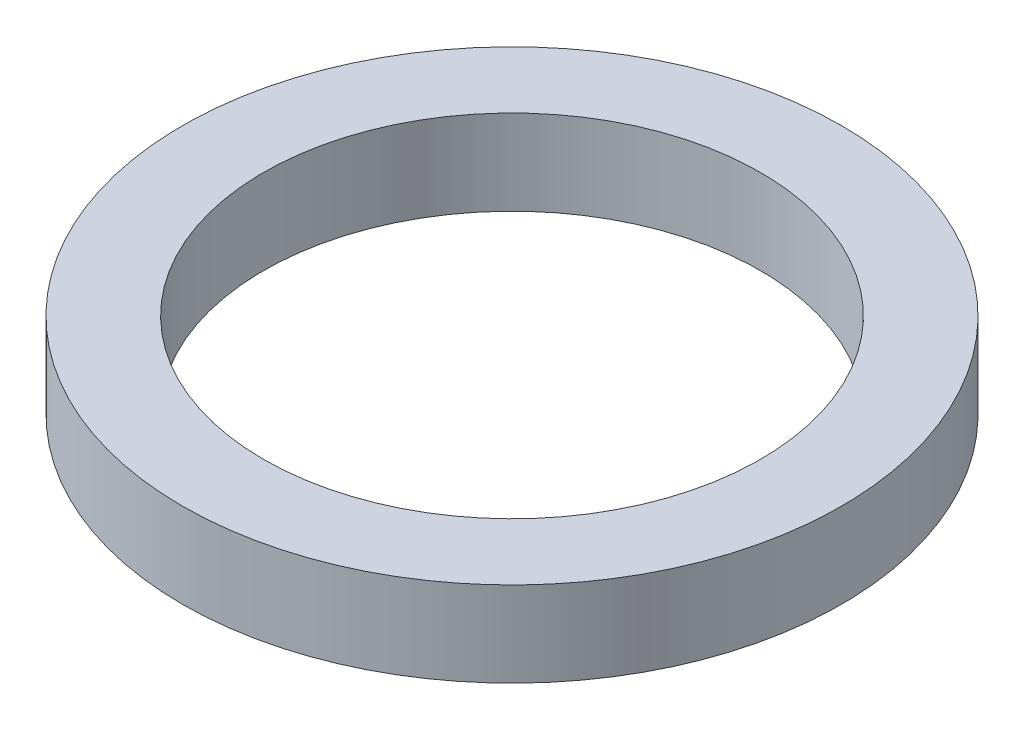
SolidWorks part; units mm, degrees
material "Alloy Steel"
ref_plane "Front Plane" through (0, 0, 0) normal (0, 0, 1) x (1, 0, 0)
ref_plane "Top Plane" through (0, 0, 0) normal (0, 1, 0) x (1, 0, 0)
ref_plane "Right Plane" through (0, 0, 0) normal (1, 0, 0) x (0, 0, -1)
sketch "Sketch1" plane through (0, 0, 0) normal (0, 1, 0) x (1, 0, 0)
  circle A0 centre (0, 0) radius 3.1496
  circle A1 centre (0, 0) radius 2.3749
  dimension "D1" = 6.2992
  dimension "D2" = 4.7498
extrude "Boss-Extrude1" add sketch "Sketch1" along normal blind 0.8128
